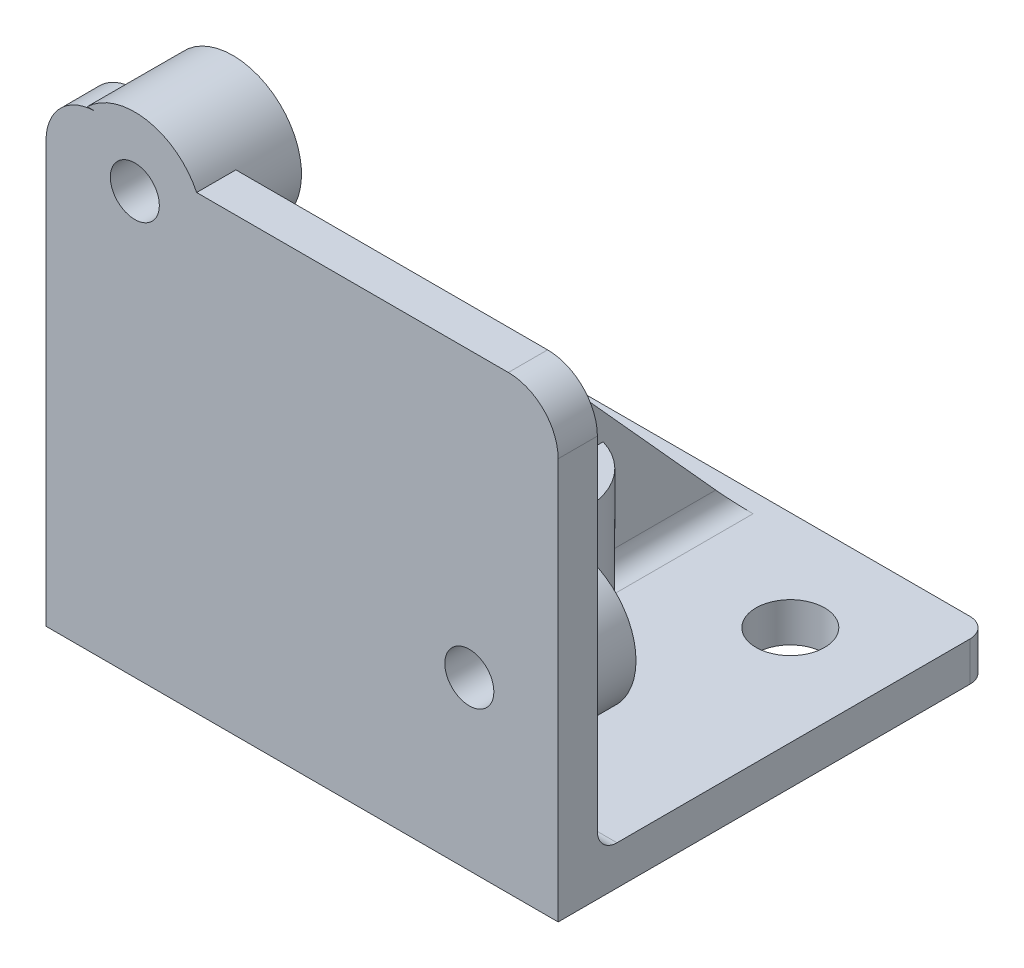
SolidWorks part; units mm, degrees
ref_plane "Front Plane" through (0, 0, 0) normal (0, 0, 1) x (1, 0, 0)
ref_plane "Top Plane" through (0, 0, 0) normal (0, 1, 0) x (1, 0, 0)
ref_plane "Right Plane" through (0, 0, 0) normal (1, 0, 0) x (0, 0, -1)
sketch "Sketch1" plane through (0, 0, 0) normal (0, 0, 1) x (1, 0, 0)
  line L1 (-28.7105, 12.6123) -> (-2.5905, 12.6123)
  line L2 (-28.7105, 12.6123) -> (-28.7105, -11.3877)
  line L3 (-28.7105, -11.3877) -> (-2.5905, -11.3877)
  line L4 (-2.5905, 12.6123) -> (-2.5905, -11.3877)
  circle A0 centre (-7.1205, -2.8577) radius 1.25
  circle A1 centre (-24.1805, 10.0923) radius 1.25
  dimension "D2" = 2.5
  dimension "D8" = 2.5
  dimension "D1" = 8.53
  dimension "D3" = 4.53
  dimension "D4" = 4.53
  dimension "D5" = 21.48
  dimension "D6" = 24
  dimension "D7" = 26.12
extrude "Boss-Extrude1" add sketch "Sketch1" along normal blind 2 contours A1 | A0 | L3 L4 L1 L2
sketch "Sketch4" plane through (0, 0, 0) normal (0, 0, -1) x (-1, 0, 0)
  line L0 (28.7105, 12.6123) -> (28.7105, -11.3877) construction
  line L1 (2.5905, -11.3877) -> (28.7105, -11.3877)
  line L2 (2.5905, -11.3877) -> (2.5905, -9.3877)
  line L3 (2.5905, -9.3877) -> (28.7105, -9.3877)
  line L4 (28.7105, -11.3877) -> (28.7105, -9.3877)
  dimension "D1" = 2
extrude "Boss-Extrude4" add sketch "Sketch4" along normal blind 20 contours L3 L4 L1 L2
fillet "Fillet2" radius 2.54 1 edges at (-28.7105, 12.6123, 1)
fillet "Fillet3" radius 1 1 edges at (-2.5905, 12.6123, 1)
fillet "Fillet4" radius 1 2 edges at (-28.7105, -10.3877, -20) (-2.5905, -10.3877, -20)
fillet "Fillet5" radius 1 1 edges
sketch "Sketch7" plane through (0, 0, 2) normal (0, 0, 1) x (1, 0, 0)
  line L0 (-26.1705, 12.6123) -> (-3.5905, 12.6123) construction
  line L1 (-26.6102, 12.6123) -> (-21.7507, 12.6123)
  arc A0 (-26.6102, 12.6123) -> (-21.7507, 12.6123) centre (-24.1805, 10.0923) cw
extrude "Boss-Extrude5" add sketch "Sketch7" against normal up to surface (2 mm away) up to face at (-15.4469, 8.3494, 0)
ref_plane "Plane1" through (-15.6505, 0, 0) normal (-1, 0, 0) x (0, 0, 1)
sketch "Sketch14" plane through (-15.6505, 0, 0) normal (-1, 0, 0) x (0, 0, 1)
  line L0 (0, 11.6123) -> (-19, -9.3877)
  line L1 (0, 11.6123) -> (0, -8.3877) construction
  line L3 (0, 11.5443) -> (0, -9.3877)
  line L4 (0, 11.5443) -> (0, 11.6123)
  line L6 (0, -9.3877) -> (-19, -9.3877)
extrude "Boss-Extrude6" add sketch "Sketch14" along normal mid plane 2
fillet "Fillet10" radius 1 6 edges at (-16.6505, 1.6123, 0) (-16.6505, -9.0949, -0.2929) (-16.6505, -9.3877, -10) (-14.6505, -9.3877, -10) (-14.6505, -9.0949, -0.2929) (-14.6505, 1.6123, 0)
sketch "Sketch15" plane through (0, -11.3877, 0) normal (0, -1, 0) x (1, 0, 0)
  line L0 (-28.7105, 2) -> (-2.5905, 2) construction
  circle A0 centre (-15.6505, -9) radius 3.5
  point P2 (-15.6505, 2)
  dimension "D1" = 11
  dimension "D2" = 7
extrude "Boss-Extrude7" add sketch "Sketch15" against normal blind 8
hole_wizard "M3.5x0.6 Tapped Hole1" positions "Sketch17" profile "Sketch18" tap size "M3.5x0.6" standard "ANSI Metric"
sketch "Sketch17" plane through (0, -11.3877, 0) normal (0, -1, 0) x (-1, 0, 0)
  point P0 (15.6505, 9)
sketch "Sketch18" plane through (-15.6505, -11.3877, -9) normal (1, 0, 0) x (0, 0, -1)
  line L0 (0, 0) -> (0, 10.8712)
  line L1 (0, 10.8712) -> (1.45, 10)
  line L2 (1.45, 10) -> (1.45, 0)
  line L5 (1.45, 0) -> (0, 0)
  line L10 (0, 10.8712) -> (-1.45, 10) construction
  line L11 (0, -6.35) -> (0, 107.95) construction
  dimension "Tap Drill Dia." = 2.9
  dimension "Tap Drill Depth" = 10
  dimension "Drill Angle" = 118
cosmetic thread "Hole Thread1" parameters "D1"=7, "D2"=3.5
sketch "Sketch19" plane through (0, 0, 0) normal (0, 0, -1) x (-1, 0, 0)
  circle A0 centre (7.1205, -2.8577) radius 3.5006
  circle A1 centre (24.1805, 10.0923) radius 3.5006
  circle A2 centre (7.1205, -2.8577) radius 1.27
  circle A3 centre (24.1805, 10.0923) radius 1.27
  arc A4 (26.6102, 12.6123) -> (21.7507, 12.6123) centre (24.1805, 10.0923) ccw construction
  dimension "D1" = 2.54
  dimension "D2" = 2.54
extrude "Boss-Extrude8" add sketch "Sketch19" along normal blind 3
sketch "Sketch20" plane through (0, 0, 0) normal (0, 0, -1) x (-1, 0, 0)
  line L0 (21.0271, 11.6123) -> (2.5905, 11.6123)
  line L1 (2.5905, 11.6123) -> (2.5905, 12.6123)
  line L2 (2.5905, 12.6123) -> (21.7507, 12.6123)
  line L3 (21.7507, 12.6123) -> (3.5905, 12.6123) construction
  arc A0 (21.7507, 12.6123) -> (26.6583, 12.565) centre (24.1805, 10.0923) ccw construction
  circle A1 centre (24.1805, 10.0923) radius 3.5006 construction
  arc A2 (21.0271, 11.6123) -> (21.7507, 12.6123) centre (24.1805, 10.0923) cw
extrude "Cut-Extrude1" cut sketch "Sketch20" against normal through all
fillet "Fillet11" radius 2.54 1 edges at (-2.5905, 11.6123, 1)
sketch "Sketch21" plane through (0, -9.3877, 0) normal (0, 1, 0) x (1, 0, 0)
  line L0 (-28.7105, 19) -> (-28.7105, 1) construction
  line L1 (-3.5905, 20) -> (-27.7105, 20) construction
  line L2 (-2.5905, 19) -> (-2.5905, 1) construction
  circle A0 centre (-23.6305, 14.92) radius 1.75
  circle A1 centre (-7.6705, 14.92) radius 1.75
  dimension "D1" = 3.5
  dimension "D2" = 5.08
  dimension "D3" = 5.08
  dimension "D4" = 5.08
extrude "Cut-Extrude2" cut sketch "Sketch21" against normal through all
